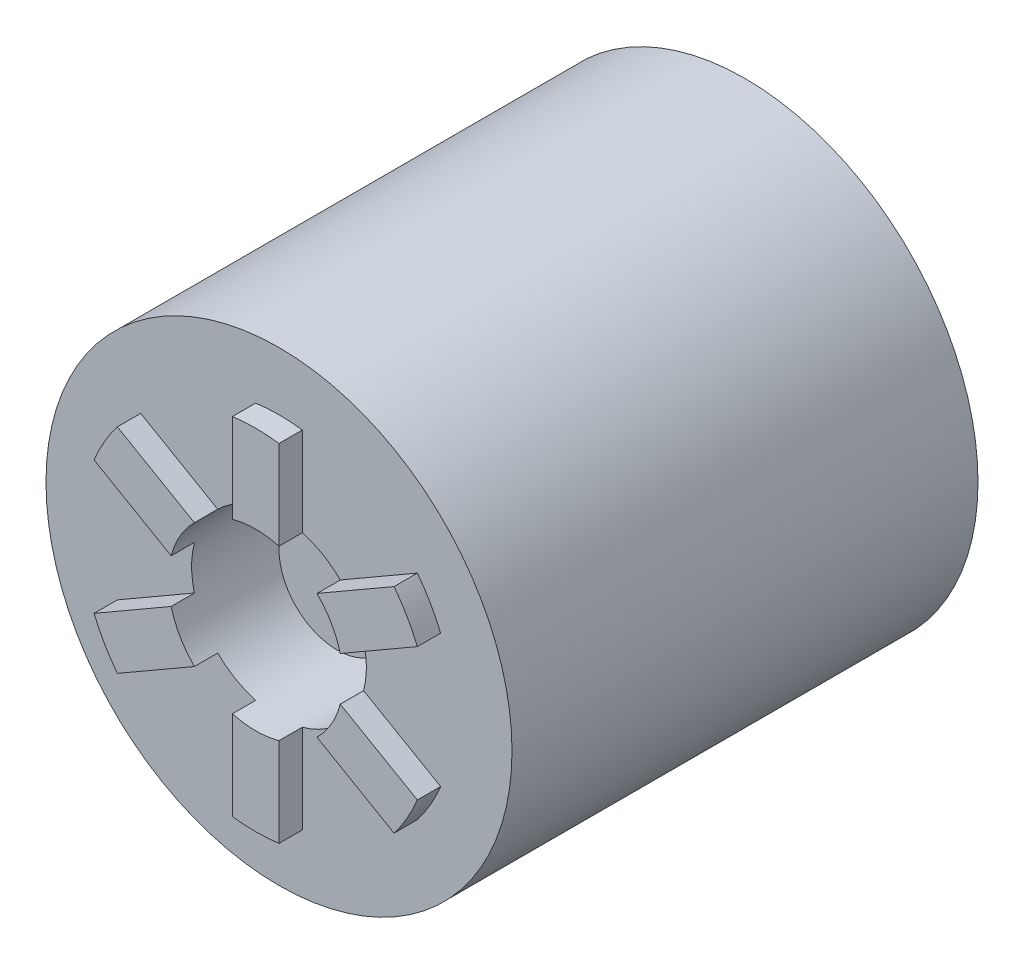
SolidWorks part; units mm, degrees
ref_plane "Front Plane" through (0, 0, 0) normal (0, 0, 1) x (1, 0, 0)
ref_plane "Top Plane" through (0, 0, 0) normal (0, 1, 0) x (1, 0, 0)
ref_plane "Right Plane" through (0, 0, 0) normal (1, 0, 0) x (0, 0, -1)
sketch "Sketch5" plane through (0, 0, 0) normal (0, 0, 1) x (1, 0, 0)
  circle A0 centre (0, 0) radius 20
  dimension "D1" = 40
extrude "Boss-Extrude3" add sketch "Sketch5" along normal blind 40
sketch "Sketch6" plane through (0, 0, 40) normal (0, 0, 1) x (1, 0, 0)
  line L0 (5.4952, 5.4821) -> (11.8744, 9.1651)
  line L1 (2, 7.5) -> (2, 14.8661)
  line L2 (-2, 7.5) -> (-2, 14.8661)
  line L3 (7.4952, 2.0179) -> (13.8744, 5.701)
  line L4 (7.4952, -2.0179) -> (13.8744, -5.701)
  line L5 (5.4952, -5.4821) -> (11.8744, -9.1651)
  line L6 (2, -7.5) -> (2, -14.8661)
  line L7 (-2, -7.5) -> (-2, -14.8661)
  line L8 (-5.4952, -5.4821) -> (-11.8744, -9.1651)
  line L9 (-7.4952, -2.0179) -> (-13.8744, -5.701)
  line L10 (-7.4952, 2.0179) -> (-13.8744, 5.701)
  line L11 (-5.4952, 5.4821) -> (-11.8744, 9.1651)
  circle A0 centre (0, 0) radius 15
  circle A1 centre (0, 0) radius 7.5
  point P7 (2, 15)
  point P9 (-2, 15)
  point P33 (0, 0)
  dimension "D1" = 30
  dimension "D2" = 15
  dimension "D3" = 6
extrude "Cut-Extrude3" cut sketch "Sketch6" against normal blind 10 contours A1
sketch "Sketch7" plane through (0, 0, 40) normal (0, 0, 1) x (1, 0, 0)
  line L0 (2, 7.2284) -> (2, 14.8661)
  line L5 (-2, 7.2284) -> (-2, 14.8661)
  line L6 (5.26, 5.3463) -> (11.8744, 9.1651)
  line L7 (7.26, 1.8822) -> (13.8744, 5.701)
  line L8 (7.26, -1.8822) -> (13.8744, -5.701)
  line L9 (5.26, -5.3463) -> (11.8744, -9.1651)
  line L10 (2, -7.2284) -> (2, -14.8661)
  line L11 (-2, -7.2284) -> (-2, -14.8661)
  line L13 (-5.26, -5.3463) -> (-11.8744, -9.1651)
  line L14 (-7.26, -1.8822) -> (-13.8744, -5.701)
  line L15 (-7.26, 1.8822) -> (-13.8744, 5.701)
  line L16 (-5.26, 5.3463) -> (-11.8744, 9.1651)
  circle A0 centre (0, 0) radius 15
  circle A1 centre (0, 0) radius 7.5 construction
  circle A2 centre (0, 0) radius 7.5
  circle A3 centre (0, 0) radius 7.5 construction
  point P18 (0, 0)
  point P35 (0, 0)
  point P39 (0, 0)
  point P46 (0, 0)
  circle M3 centre (0, 0) radius 7.5
  dimension "D1" = 30
  dimension "D2" = 6
extrude "Boss-Extrude4" add sketch "Sketch7" along normal blind 2 contours L0 A0 L5 M3 | L7 A0 L6 M3 | L9 A0 L8 M3 | L11 A0 L10 M3 | L14 A0 L13 M3 | L16 A0 L15 M3
sketch "Sketch8" plane through (0, 0, 0) normal (0, 0, -1) x (-1, 0, 0)
  circle A1 centre (0, 0) radius 5
  dimension "D2" = 10
extrude "Cut-Extrude6" cut sketch "Sketch8" against normal blind 25
sketch "Sketch9" plane through (0, 0, 0) normal (0, 0, -1) x (-1, 0, 0)
  circle A0 centre (0, 0) radius 12.5
  dimension "D1" = 25
extrude "Cut-Extrude7" cut sketch "Sketch9" against normal blind 5
sketch "Sketch10" plane through (0, 0, 30) normal (0, 0, 1) x (1, 0, 0)
  circle A0 centre (0, 0) radius 5
  dimension "D1" = 10
extrude "Boss-Extrude5" add sketch "Sketch10" along normal blind 5
